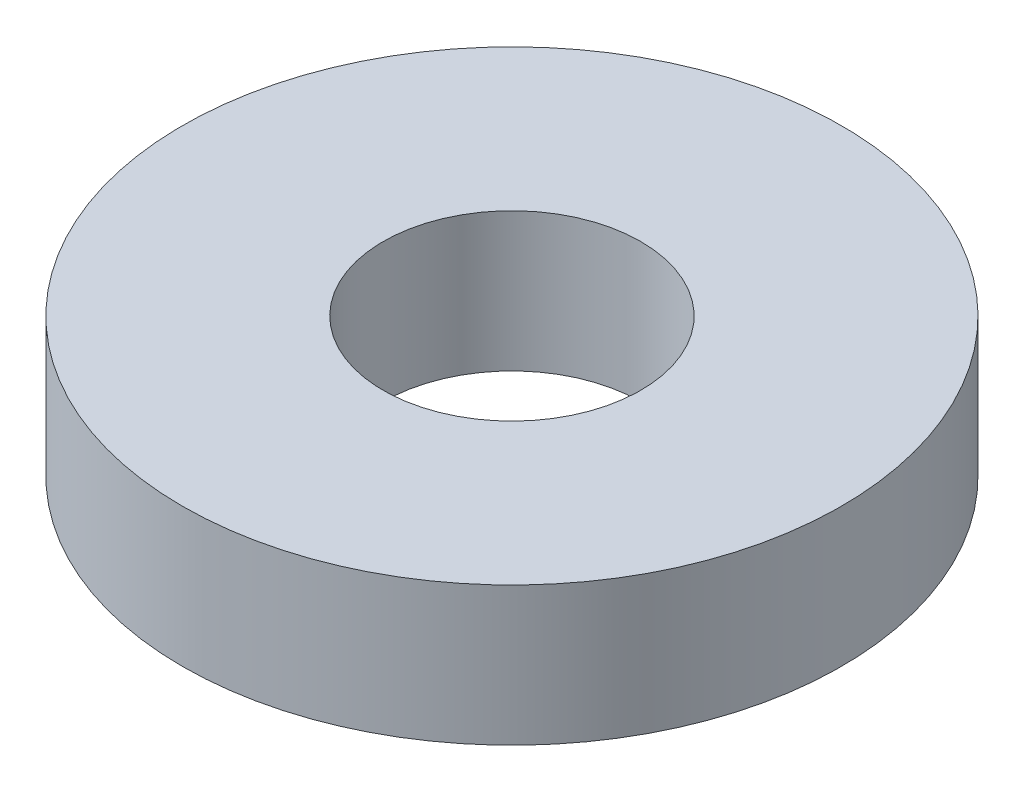
SolidWorks part; units mm, degrees
ref_plane "Front Plane" through (0, 0, 0) normal (0, 0, 1) x (1, 0, 0)
ref_plane "Top Plane" through (0, 0, 0) normal (0, 1, 0) x (1, 0, 0)
ref_plane "Right Plane" through (0, 0, 0) normal (1, 0, 0) x (0, 0, -1)
sketch "Sketch1" plane through (0, 0, 0) normal (0, 1, 0) x (1, 0, 0)
  circle A0 centre (0, 0) radius 8.4455
extrude "Boss-Extrude1" add sketch "Sketch1" along normal blind 3.556
sketch "Sketch2" plane through (0, 0, 0) normal (0, -1, 0) x (-1, 0, 0)
  circle A0 centre (0, 0) radius 3.302
extrude "Cut-Extrude1" cut sketch "Sketch2" against normal through all
